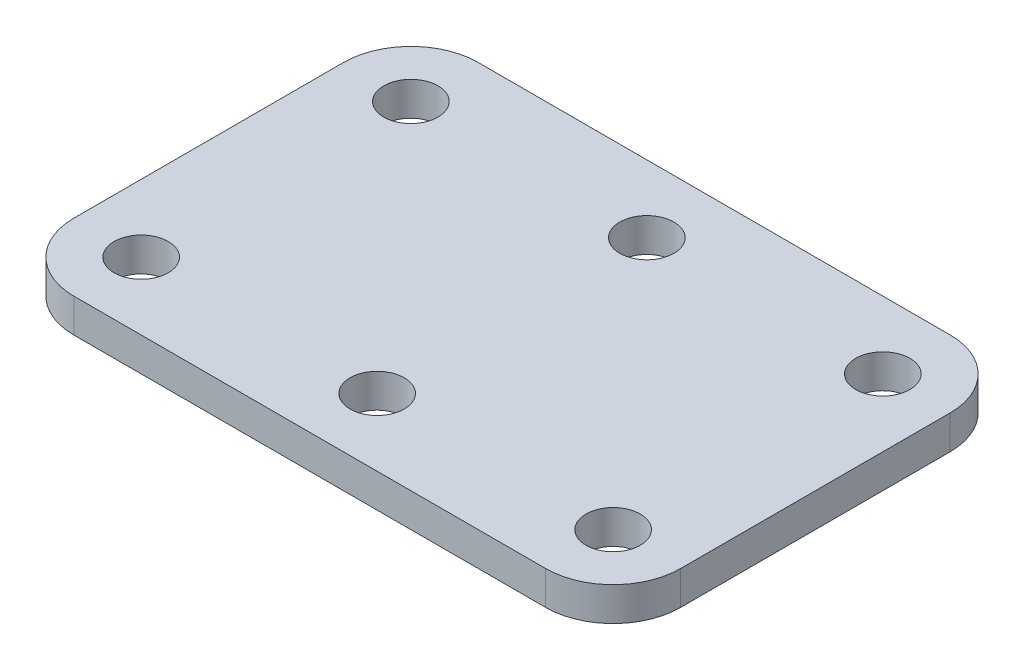
SolidWorks part; units mm, degrees
ref_plane "Front" through (0, 0, 0) normal (0, 0, 1) x (1, 0, 0)
ref_plane "Top" through (0, 0, 0) normal (0, 1, 0) x (1, 0, 0)
ref_plane "Right" through (0, 0, 0) normal (1, 0, 0) x (0, 0, -1)
sketch "Sketch1" plane through (0, 0, 0) normal (0, 1, 0) x (1, 0, 0)
  line L1 (22.225, -19.05) -> (-22.225, -19.05)
  line L2 (28.575, -12.7) -> (28.575, 12.7)
  line L3 (22.225, 19.05) -> (-22.225, 19.05)
  line L4 (-28.575, -12.7) -> (-28.575, 12.7)
  line L5 (28.575, -19.05) -> (-28.575, 19.05) construction
  line L6 (28.575, 19.05) -> (-28.575, -19.05) construction
  arc A0 (28.575, 12.7) -> (22.225, 19.05) centre (22.225, 12.7) ccw
  arc A1 (22.225, -19.05) -> (28.575, -12.7) centre (22.225, -12.7) ccw
  arc A2 (-22.225, -19.05) -> (-28.575, -12.7) centre (-22.225, -12.7) cw
  arc A3 (-22.225, 19.05) -> (-28.575, 12.7) centre (-22.225, 12.7) ccw
  point P0 (0, 0)
  dimension "D3" = 6.35
  dimension "D1" = 57.15
  dimension "D2" = 38.1
extrude "Boss-Extrude1" add sketch "Sketch1" along normal blind 3.175
sketch "Sketch4" plane through (0, 3.175, 0) normal (0, 1, 0) x (1, 0, 0)
  arc A0 (22.225, -19.05) -> (28.575, -12.7) centre (22.225, -12.7) ccw construction
  point P0 (-22.225, 12.7)
  point P11 (0, 12.7)
  point P12 (22.225, 12.7)
  point P13 (0, -12.7)
  point P14 (22.225, -12.7)
  point P15 (-22.225, -12.7)
  dimension "D1" = 3
  dimension "D2" = 2
hole_wizard "#10 Clearance Hole1" positions "Sketch4" profile "Sketch3" hole size "#10" standard "ANSI Inch" end condition through all
sketch "Sketch3" plane through (-22.225, 3.175, -12.7) normal (1, 0, 0) x (0, 0, 1)
  line L0 (0, 0) -> (0, 3.175)
  line L1 (0, 3.175) -> (2.5527, 3.175)
  line L2 (2.5527, 3.175) -> (2.5527, 0)
  line L5 (2.5527, 0) -> (0, 0)
  line L11 (0, -6.35) -> (0, 107.95) construction
  dimension "Thru Hole Dia." = 5.1054
  dimension "Thru Hole Depth" = 3.175
